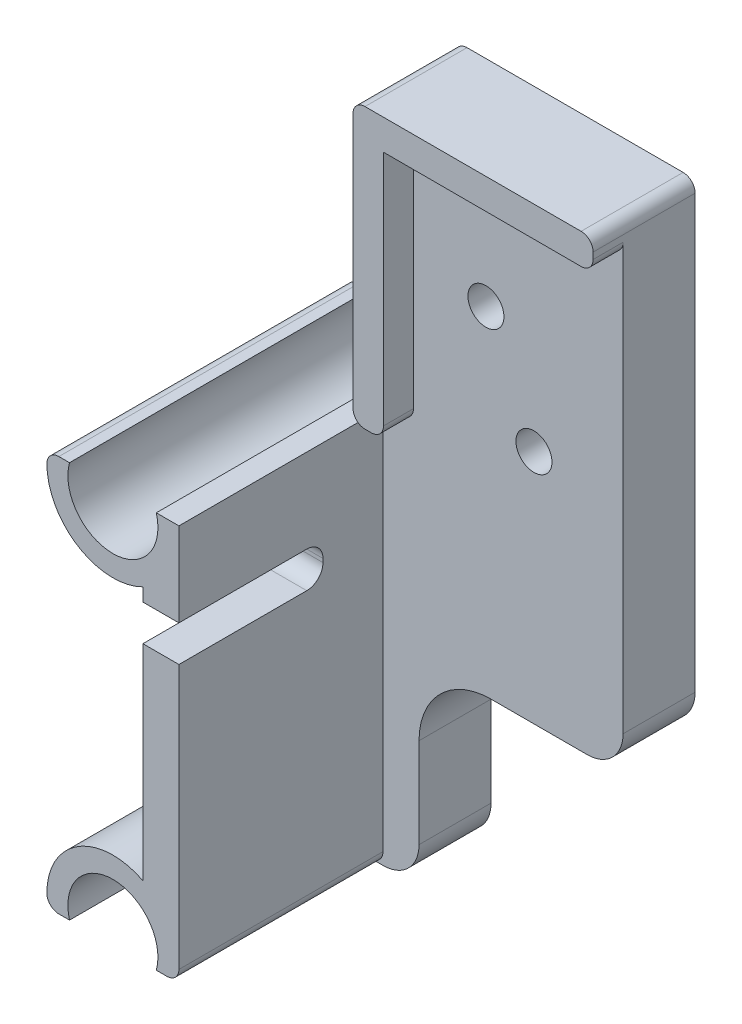
SolidWorks part; units mm, degrees
ref_plane "Front Plane" through (0, 0, 0) normal (0, 0, 1) x (1, 0, 0)
ref_plane "Top Plane" through (0, 0, 0) normal (0, 1, 0) x (1, 0, 0)
ref_plane "Right Plane" through (0, 0, 0) normal (1, 0, 0) x (0, 0, -1)
sketch "Sketch1" plane through (0, 0, 0) normal (0, 0, 1) x (1, 0, 0)
  line L0 (-21, 16.5) -> (-21, -16.5)
  line L1 (-15.5, 15.5) -> (15.5, 15.5) construction
  line L2 (-15.5, 15.5) -> (-15.5, -15.5) construction
  line L3 (-15.5, -15.5) -> (15.5, -15.5) construction
  line L4 (15.5, 15.5) -> (15.5, -15.5) construction
  line L5 (-15.5, 15.5) -> (15.5, -15.5) construction
  line L6 (-15.5, -15.5) -> (15.5, 15.5) construction
  line L7 (-21, 21) -> (21, 21) construction
  line L8 (-21, 21) -> (-21, -21) construction
  line L9 (-21, -21) -> (21, -21) construction
  line L10 (21, 21) -> (21, -21) construction
  line L11 (-21, 21) -> (21, -21) construction
  line L12 (-21, -21) -> (21, 21) construction
  line L13 (-16.5, 21) -> (16.5, 21) construction
  line L14 (-21, 16.5) -> (-16.5, 21)
  line L15 (-16.5, -21) -> (16.5, -21)
  line L16 (21, 16.5) -> (21, -16.5)
  line L17 (-21, -16.5) -> (-16.5, -21)
  line L18 (16.5, -21) -> (21, -16.5)
  line L19 (21, 16.5) -> (16.5, 21)
  line L20 (-18, 0) -> (-21, 0) construction
  line L21 (-10.601, 18) -> (10.601, 18) construction
  line L22 (-10.601, 18) -> (-10.601, -18) construction
  line L23 (-10.601, -18) -> (10.601, -18)
  line L24 (10.601, 18) -> (10.601, -18) construction
  line L25 (-18, 10.601) -> (18, 10.601) construction
  line L26 (-18, 10.601) -> (-18, -10.601)
  line L27 (-18, -10.601) -> (18, -10.601) construction
  line L28 (18, 10.601) -> (18, -10.601)
  line L29 (-18, 10.601) -> (18, -10.601) construction
  line L30 (-18, -10.601) -> (18, 10.601) construction
  line L31 (-10.601, 18) -> (10.601, -18) construction
  line L32 (-10.601, -18) -> (10.601, 18) construction
  line L33 (0, -18) -> (0, -21) construction
  line L34 (-11.125, 21) -> (11.125, 21) construction
  line L35 (-16.5, 21) -> (-11.125, 21)
  line L36 (11.125, 21) -> (16.5, 21)
  line L37 (-11.125, 21) -> (-11.125, 18)
  line L38 (-11.125, 18) -> (-10.601, 18)
  line L39 (11.125, 21) -> (11.125, 18)
  line L40 (11.125, 18) -> (10.601, 18)
  line L41 (16.5, 21) -> (21, 21) construction
  line L42 (21, 21) -> (21, 16.5) construction
  line L43 (16.5, -21) -> (21, -21) construction
  line L44 (21, -21) -> (21, -16.5) construction
  circle A0 centre (-15.5, 15.5) radius 3.75
  circle A1 centre (15.5, 15.5) radius 3.75
  circle A2 centre (15.5, -15.5) radius 3.75
  circle A3 centre (-15.5, -15.5) radius 3.75
  circle A4 centre (-15.5, 15.5) radius 5.5 construction
  circle A5 centre (15.5, 15.5) radius 5.5 construction
  circle A6 centre (15.5, -15.5) radius 5.5 construction
  circle A7 centre (-15.5, -15.5) radius 5.5 construction
  arc A8 (-18, 10.601) -> (-10.601, 18) centre (-15.5, 15.5) ccw
  arc A9 (10.601, 18) -> (18, 10.601) centre (15.5, 15.5) ccw
  arc A10 (-18, -10.601) -> (-10.601, -18) centre (-15.5, -15.5) cw
  arc A11 (10.601, -18) -> (18, -10.601) centre (15.5, -15.5) cw
  point P0 (0, 0)
  point P14 (0, 0)
  point P22 (-21, 0)
  point P25 (0, 21)
  point P28 (0, -21)
  point P31 (21, 0)
  point P32 (0, 0)
  point P40 (0, 0)
  point P52 (0, 21)
  dimension "D1" = 7.5
  dimension "D2" = 11
  dimension "D3" = 31
  dimension "D4" = 42
  dimension "D5" = 33
  dimension "D6" = 22.25
extrude "Boss-Extrude1" add sketch "Sketch1" along normal blind 25
fillet "Fillet1" radius 2 4 edges at (-21, -16.5, 12.5) (-16.5, 21, 12.5) (-21, 16.5, 12.5) (-16.5, -21, 12.5)
sketch "Sketch3" plane through (0, -21, 0) normal (0, -1, 0) x (-1, 0, 0)
  line L0 (0, -25) -> (0, 0) construction
  line L5 (0, -25) -> (0, -22) construction
  line L6 (-10, -3) -> (10, -3)
  line L7 (-10, -3) -> (-10, -22)
  line L8 (-10, -22) -> (10, -22)
  line L9 (10, -3) -> (10, -22)
  line L10 (-10, -3) -> (10, -22) construction
  line L11 (-10, -22) -> (10, -3) construction
  point P5 (0, -12.5)
  dimension "D2" = 20
  dimension "D1" = 3
extrude "Cut-Extrude2" cut sketch "Sketch3" against normal blind 6
fillet "Fillet2" radius 3 4 edges at (10, -19.5, 3) (-10, -19.5, 3) (-10, -19.5, 22) (10, -19.5, 22)
sketch "Sketch7" plane through (0, 0, 25) normal (0, 0, 1) x (1, 0, 0)
  line L1 (10, -21) -> (-22.0583, -21)
  line L2 (10, -21) -> (10, 21.5368)
  line L3 (10, 21.5368) -> (-22.0583, 21.5368)
  line L4 (-22.0583, -21) -> (-22.0583, 21.5368)
extrude "Cut-Extrude5" cut sketch "Sketch7" against normal blind 25
sketch "Sketch10" plane through (0, 0, 25) normal (0, 0, 1) x (1, 0, 0)
  line L1 (21, 16.5) -> (8.7457, 16.5)
  line L2 (21, 16.5) -> (21, 22.2483)
  line L3 (21, 22.2483) -> (8.7457, 22.2483)
  line L4 (8.7457, 16.5) -> (8.7457, 22.2483)
  line L5 (21, -16.5) -> (7.3183, -16.5)
  line L6 (21, -16.5) -> (21, -22.0036)
  line L7 (21, -22.0036) -> (7.3183, -22.0036)
  line L8 (7.3183, -16.5) -> (7.3183, -22.0036)
extrude "Cut-Extrude6" cut sketch "Sketch10" against normal up to vertex (25 mm away)
sketch "Sketch11" plane through (21, 0, 0) normal (1, 0, 0) x (0, 0, -1)
  line L0 (-25, -16.5) -> (0, -16.5) construction
  line L1 (-2, 40) -> (-8, 40)
  line L2 (-2, 40) -> (-2, -16.5)
  line L3 (-2, -16.5) -> (-8, -16.5)
  line L4 (-8, 40) -> (-8, -16.5)
  line L5 (-2, 40) -> (-8, -16.5) construction
  line L6 (-2, -16.5) -> (-8, 40) construction
  line L8 (-2, -16.5) -> (0, -16.5) construction
  point P4 (-5, 11.75)
  dimension "D1" = 6
  dimension "D2" = 2
extrude "Boss-Extrude2" add sketch "Sketch11" along normal blind 20
sketch "Sketch13" plane through (21, 0, 0) normal (1, 0, 0) x (0, 0, -1)
  line L1 (-25, 9.5) -> (-14.35, 9.5)
  line L2 (-25, 9.5) -> (-25, 6.5)
  line L3 (-25, 6.5) -> (-14.35, 6.5)
  line L4 (-13, 8.15) -> (-13, 7.85)
  line L5 (-25, 9.5) -> (-13, 6.5) construction
  line L6 (-25, 6.5) -> (-13, 9.5) construction
  line L8 (-14.35, 6.5) -> (-14.35, 7.85) construction
  line L9 (-14.35, 7.85) -> (-14.35, 8.15) construction
  line L10 (-14.35, 8.15) -> (-14.35, 9.5) construction
  line L13 (-25, 9.5) -> (-25, 16.5) construction
  arc A0 (-14.35, 6.5) -> (-13, 7.85) centre (-14.35, 7.85) ccw
  arc A1 (-14.35, 9.5) -> (-13, 8.15) centre (-14.35, 8.15) cw
  point P4 (-19, 8)
  dimension "D3" = 1.35
  dimension "D1" = 3
  dimension "D2" = 12
  dimension "D4" = 7
extrude "Cut-Extrude9" cut sketch "Sketch13" against normal up to vertex (3 mm away)
sketch "Sketch15" plane through (0, 0, 8) normal (0, 0, 1) x (1, 0, 0)
  line L0 (21, 16.5) -> (21, -16.5) construction
  line L1 (24, -16.5) -> (24, -6)
  line L2 (41, -16.5) -> (21, -16.5) construction
  line L3 (24, -16.5) -> (21, -16.5) construction
  line L4 (30, 0) -> (41, 0)
  line L5 (41, 40) -> (41, -16.5) construction
  line L9 (24, -16.5) -> (41, -16.5)
  line L10 (41, -16.5) -> (41, 0)
  arc A0 (24, -6) -> (30, 0) centre (30, -6) cw
  dimension "D1" = 6
  dimension "D2" = 3
extrude "Cut-Extrude11" cut sketch "Sketch15" against normal blind 10
sketch "Sketch16" plane through (0, 0, 8) normal (0, 0, 1) x (1, 0, 0)
  line L0 (41, 40) -> (41, 0) construction
  line L1 (21, 40) -> (41, 40)
  line L2 (21, 40) -> (21, 37.4788)
  line L4 (41, 40) -> (41, 37.4618)
  line L5 (21, 40) -> (41, 37.4618) construction
  line L6 (21, 37.4788) -> (41, 40) construction
  line L7 (21, 37.4788) -> (21, 16.7265)
  line L9 (21, 16.7265) -> (23.5382, 16.7265)
  line L10 (23.5382, 16.7265) -> (23.5382, 37.4788)
  line L11 (23.5382, 37.4788) -> (41, 37.4618)
  line L12 (21, 37.4788) -> (23.5382, 37.4788) construction
  line L13 (41, 40) -> (21, 40) construction
  line L14 (21, 40) -> (21, 16.5) construction
  point P4 (30.9664, 38.7352)
extrude "Boss-Extrude3" add sketch "Sketch16" along normal blind 2.5
fillet "Fillet5" radius 3 2 edges at (41, 0, 5) (24, -16.5, 5)
fillet "Fillet6" radius 1 10 edges at (21, -16.5, 1) (21, 16.5, 1) (41, 40, 6.25) (21, 40, 6.25) (10.0917, -16.5, 12.5) (10.0917, 16.5, 12.5) (21, 16.7265, 9.25) (23.5382, 16.7265, 9.25) (41, 37.4618, 9.25) (21, -16.5, 16.5)
sketch "Sketch17" plane through (0, 0, 8) normal (0, 0, 1) x (1, 0, 0)
  line L0 (29.5742, 32.7543) -> (29.5742, 25.4633) construction
  line L1 (33.5742, 24.2543) -> (33.5742, 16.9633) construction
  arc A0 (31.0742, 31.2543) -> (28.0742, 31.2543) centre (29.5742, 31.2543) ccw construction
  arc A1 (28.0742, 26.9633) -> (31.0742, 26.9633) centre (29.5742, 26.9633) ccw construction
  arc A2 (35.0742, 22.7543) -> (32.0742, 22.7543) centre (33.5742, 22.7543) ccw construction
  arc A3 (32.0742, 18.4633) -> (35.0742, 18.4633) centre (33.5742, 18.4633) ccw construction
  circle A4 centre (29.5742, 28.1157) radius 1.5
  circle A5 centre (33.5742, 19.6429) radius 1.5
  point P20 (0, 0)
  point P21 (0, 0)
  point P22 (33.3168, 19.6429)
  dimension "D1" = 3
extrude "Cut-Extrude12" cut sketch "Sketch17" against normal blind 10
sketch "Sketch18" plane through (0, 0, 0) normal (0, 0, -1) x (-1, 0, 0)
  circle A0 centre (-33.5742, 19.6429) radius 2
  circle A1 centre (-29.5742, 28.1157) radius 2
  dimension "D1" = 4
extrude "Cut-Extrude13" [suppressed] cut sketch "Sketch18" against normal blind 3
